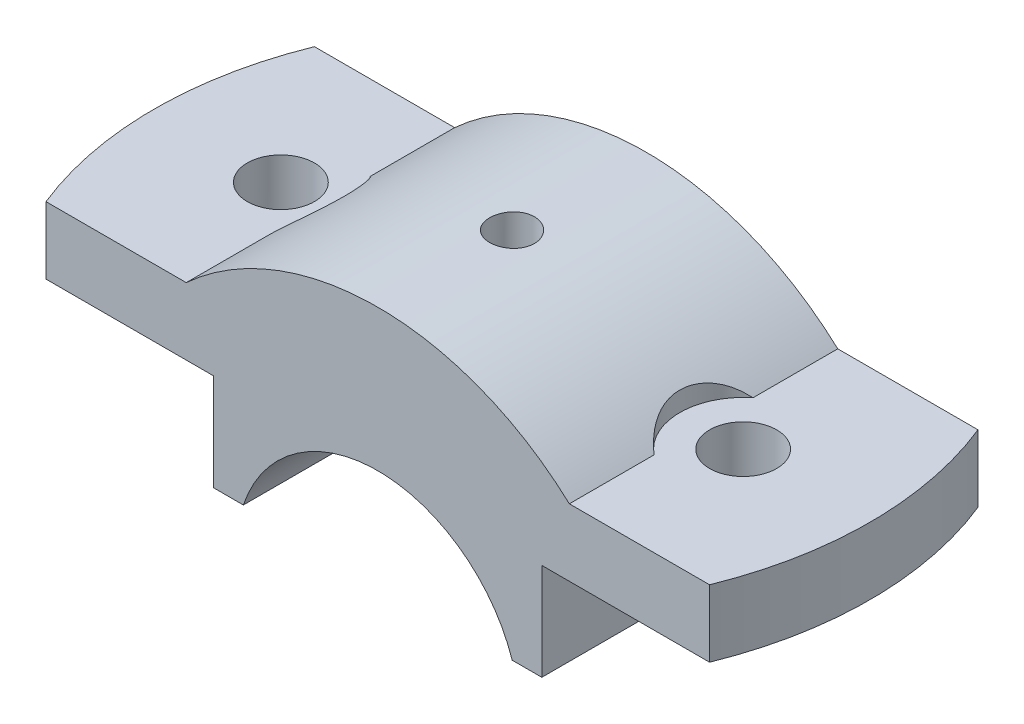
SolidWorks part; units mm, degrees
ref_plane "Front Plane" through (0, 0, 0) normal (0, 0, 1) x (1, 0, 0)
ref_plane "Top Plane" through (0, 0, 0) normal (0, 1, 0) x (1, 0, 0)
ref_plane "Right Plane" through (0, 0, 0) normal (1, 0, 0) x (0, 0, -1)
sketch "Sketch2" plane through (0, 0, 0) normal (0, 0, 1) x (1, 0, 0)
  line L0 (0, 0) -> (0, 83.9016) construction
  line L1 (18.0278, 6) -> (22, 6)
  line L2 (22, 6) -> (22, 19)
  line L3 (22, 19) -> (50, 19)
  line L4 (50, 19) -> (50, 28)
  line L5 (50, 28) -> (25.6905, 28)
  line L6 (-18.0278, 6) -> (-22, 6)
  line L7 (-22, 6) -> (-22, 19)
  line L8 (-22, 19) -> (-50, 19)
  line L9 (-50, 19) -> (-50, 28)
  line L10 (-50, 28) -> (-25.6905, 28)
  arc A0 (-18.0278, 6) -> (18.0278, 6) centre (0, 0) cw
  arc A1 (-25.6905, 28) -> (25.6905, 28) centre (0, 0) cw
  dimension "D1" = 6
  dimension "D5" = 19
  dimension "D6" = 38
  dimension "D2" = 13
  dimension "D3" = 9
  dimension "D4" = 44
  dimension "D7" = 100
extrude "Boss-Extrude1" add sketch "Sketch2" along normal mid plane 36 contours A1 L5 L4 L3 L2 L1 A0 L6 L7 L8 L9 L10
hole_wizard "Ø1.0mm Dowel Hole1" positions "Sketch6" profile "Sketch5" hole size "Ø1.0" standard "ANSI Metric" end condition through all
sketch "Sketch6" plane through (0, 28, 0) normal (0, 1, 0) x (1, 0, 0)
  point P0 (31, 0)
sketch "Sketch5" plane through (31, 28, 0) normal (1, 0, 0) x (0, 0, 1)
  line L0 (0, 0) -> (0, 22)
  line L1 (0, 22) -> (4.5, 22)
  line L2 (4.5, 22) -> (4.5, 0)
  line L5 (4.5, 0) -> (0, 0)
  line L11 (0, -6.35) -> (0, 107.95) construction
  dimension "Thru Hole Dia." = 9
  dimension "Thru Hole Depth" = 22
sketch "Sketch7" plane through (0, 28, 0) normal (0, 1, 0) x (1, 0, 0)
  line L0 (50, 18) -> (25.6905, 18) construction
  line L1 (50, -18) -> (50, 18) construction
  line L2 (50, -18) -> (25.6905, -18) construction
  line L3 (50, 18) -> (44.4972, 18)
  line L4 (50, -18) -> (50, 18)
  line L5 (50, -18) -> (44.4972, -18)
  arc A0 (44.4972, -18) -> (44.4972, 18) centre (0, 0) ccw
  dimension "D1" = 96
extrude "Cut-Extrude1" cut sketch "Sketch7" against normal blind 36
hole_wizard "Ø1.0mm Dowel Hole2" positions "3DSketch2" profile "Sketch9" hole size "Ø1.0" standard "ANSI Metric"
sketch3d "3DSketch2"
  point P0 (0, 0, 0)
  point P3 (0, 38, 0)
  dimension "D1" = 0
  dimension "D2" = 0
sketch "Sketch9" plane through (0, 38, 0) normal (1, 0, 0) x (0, 0, 1)
  line L0 (0, 0) -> (0, 14.8026)
  line L1 (0, 14.8026) -> (3, 13)
  line L2 (3, 13) -> (3, 0)
  line L5 (3, 0) -> (0, 0)
  line L10 (0, 14.8026) -> (-3, 13) construction
  line L11 (0, -6.35) -> (0, 107.95) construction
  dimension "Hole Dia." = 6
  dimension "Hole Depth" = 13
  dimension "Drill Angle" = 118
hole_wizard "Ø1.0mm Dowel Hole4" positions "3DSketch5" profile "Sketch13" hole size "Ø1.0" standard "ANSI Metric" end condition through all
sketch3d "3DSketch5"
  point P0 (0, 0, 0)
  point P3 (0, 19, 0)
  dimension "D1" = 0
  dimension "D2" = 0
sketch "Sketch13" plane through (0, 19, 0) normal (1, 0, 0) x (0, 0, -1)
  line L0 (0, 0) -> (0, 19)
  line L1 (0, 19) -> (2.5, 19)
  line L2 (2.5, 19) -> (2.5, 0)
  line L5 (2.5, 0) -> (0, 0)
  line L11 (0, -6.35) -> (0, 107.95) construction
  dimension "Thru Hole Dia." = 5
  dimension "Thru Hole Depth" = 19
mirror "Mirror1" about plane through (0, 0, 0) normal (1, 0, 0) of "Cut-Extrude1", "Ø1.0mm Dowel Hole1"
sketch "Sketch16" plane through (0, 28, 0) normal (0, 1, 0) x (1, 0, 0)
  line L0 (-25.6905, -18) -> (-25.6905, 18) construction
  line L1 (-25.6905, -6.6377) -> (-25.6905, 6.6377)
  arc A0 (-25.6905, -6.6377) -> (-25.6905, 6.6377) centre (-31, 0) ccw
  dimension "D1" = 17
extrude "Cut-Extrude2" cut sketch "Sketch16" along normal blind 10
mirror "Mirror2" about plane through (0, 0, 0) normal (1, 0, 0) of "Cut-Extrude2"
